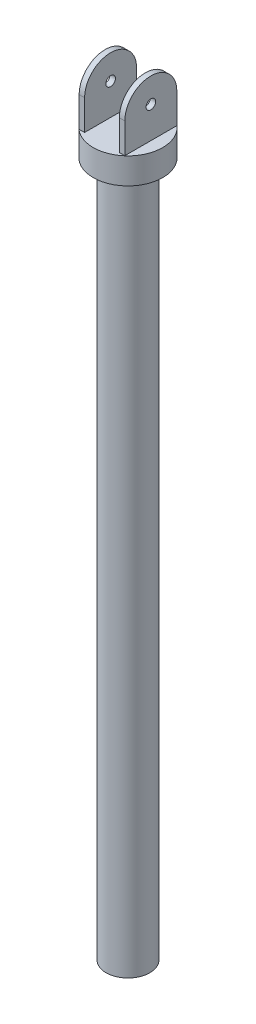
SolidWorks part; units mm, degrees
ref_plane "Front Plane" through (0, 0, 0) normal (0, 0, 1) x (1, 0, 0)
ref_plane "Top Plane" through (0, 0, 0) normal (0, 1, 0) x (1, 0, 0)
ref_plane "Right Plane" through (0, 0, 0) normal (1, 0, 0) x (0, 0, -1)
sketch "Sketch1" plane through (0, 0, 0) normal (0, 1, 0) x (1, 0, 0)
  circle A0 centre (0, 0) radius 25.4
  dimension "D1" = 50.8
extrude "Boss-Extrude1" add sketch "Sketch1" along normal blind 19.05
ref_plane "Plane1" through (12.7, 0, 0) normal (1, 0, 0) x (0, 0, -1)
sketch "Sketch2" plane through (12.7, 0, 0) normal (1, 0, 0) x (0, 0, -1)
  line L0 (-19, 19.05) -> (19, 19.05)
  line L2 (19, 19.05) -> (19, 41.05)
  line L3 (0, 42.05) -> (0, 0) construction
  line L4 (-19, 41.05) -> (-19, 19.05)
  circle A0 centre (0, 42.05) radius 3.5
  arc A1 (19, 41.05) -> (-19, 41.05) centre (0, 41.05) ccw
  point P4 (0, 60.05)
  dimension "D4" = 7
  dimension "D2" = 23
  dimension "D3" = 41
  dimension "D5" = 38
extrude "Boss-Extrude2" add sketch "Sketch2" along normal blind 4
mirror "Mirror1" about plane through (0, 0, 0) normal (1, 0, 0) of "Boss-Extrude2"
sketch "Sketch3" plane through (0, 0, 0) normal (0, -1, 0) x (1, 0, 0)
  circle A0 centre (0, 0) radius 16
  dimension "D1" = 32
extrude "Boss-Extrude3" add sketch "Sketch3" along normal blind 508
